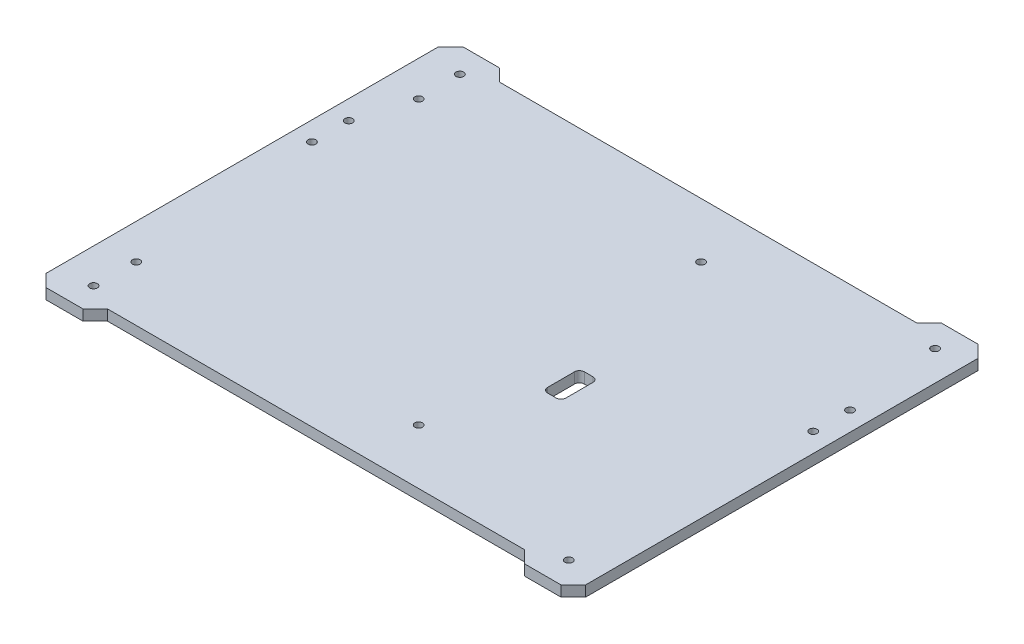
SolidWorks part; units mm, degrees
ref_plane "Front Plane" through (0, 0, 0) normal (0, 0, 1) x (1, 0, 0)
ref_plane "Top Plane" through (0, 0, 0) normal (0, 1, 0) x (1, 0, 0)
ref_plane "Right Plane" through (0, 0, 0) normal (1, 0, 0) x (0, 0, -1)
sketch "Sketch1" plane through (0, 0, 0) normal (0, 1, 0) x (1, 0, 0)
  line L1 (0, 0) -> (279.4, 0)
  line L2 (0, 0) -> (0, 215.9)
  line L3 (0, 215.9) -> (279.4, 215.9)
  line L4 (279.4, 0) -> (279.4, 215.9)
  dimension "D1" = 279.4
  dimension "D2" = 215.9
extrude "Boss-Extrude1" add sketch "Sketch1" along normal blind 5.5118
hole_wizard "5/32 (0.15625) Diameter Hole1" positions "Sketch3" profile "Sketch2" hole size "5/32" standard "ANSI Inch" end condition through all
sketch "Sketch3" plane through (0, 5.5118, 0) normal (0, 1, 0) x (1, 0, 0)
  line L0 (0, 0) -> (279.4, 0) construction
  line L1 (0, 215.9) -> (0, 0) construction
  line L2 (279.4, 215.9) -> (0, 215.9) construction
  line L3 (139.7, 215.9) -> (139.7, 0) construction
  point P0 (17.8594, 13.0969)
  point P7 (17.8594, 202.8031)
  point P9 (9.9219, 153.1938)
  point P11 (9.9219, 134.1438)
  point P27 (263.9219, 13.0969)
  point P28 (269.4781, 134.1438)
  point P29 (269.4781, 153.1938)
  point P30 (263.9219, 202.8031)
  dimension "D1" = 13.0969
  dimension "D2" = 134.1438
  dimension "D3" = 19.05
  dimension "D4" = 9.9219
  dimension "D5" = 13.0969
  dimension "D6" = 17.8594
  dimension "D7" = 246.0625
sketch "Sketch2" plane through (17.8594, 5.5118, -13.0969) normal (1, 0, 0) x (0, 0, 1)
  line L0 (0, 0) -> (0, 5.5118)
  line L1 (0, 5.5118) -> (1.9844, 5.5118)
  line L2 (1.9844, 5.5118) -> (1.9844, 0)
  line L5 (1.9844, 0) -> (0, 0)
  line L11 (0, -6.35) -> (0, 107.95) construction
  dimension "Thru Hole Dia." = 3.9688
  dimension "Thru Hole Depth" = 5.5118
hole_wizard "5/32 (0.15625) Diameter Hole2" positions "Sketch5" profile "Sketch4" hole size "5/32" standard "ANSI Inch" end condition through all
sketch "Sketch5" plane through (0, 5.5118, 0) normal (0, 1, 0) x (1, 0, 0)
  line L0 (0, 215.9) -> (0, 0) construction
  line L2 (0, 107.95) -> (279.4, 107.95) construction
  line L3 (279.4, 0) -> (279.4, 215.9) construction
  point P0 (18.2563, 34.8361)
  point P2 (164.4841, 34.8361)
  point P17 (164.4841, 181.0639)
  point P18 (18.2563, 181.0639)
  dimension "D1" = 18.2562
  dimension "D2" = 146.2278
  dimension "D3" = 73.1139
sketch "Sketch4" plane through (18.2563, 5.5118, -34.8361) normal (1, 0, 0) x (0, 0, 1)
  line L0 (0, 0) -> (0, 5.5118)
  line L1 (0, 5.5118) -> (1.9844, 5.5118)
  line L2 (1.9844, 5.5118) -> (1.9844, 0)
  line L5 (1.9844, 0) -> (0, 0)
  line L11 (0, -6.35) -> (0, 107.95) construction
  dimension "Thru Hole Dia." = 3.9688
  dimension "Thru Hole Depth" = 5.5118
sketch "Sketch6" plane through (0, 5.5118, 0) normal (0, 1, 0) x (1, 0, 0)
  line L0 (279.4, 215.9) -> (0, 215.9) construction
  line L4 (279.4, 215.9) -> (0, 215.9)
  line L5 (0, 107.95) -> (279.4, 107.95) construction
  line L6 (0, 215.9) -> (0, 0) construction
  line L7 (279.4, 0) -> (279.4, 215.9) construction
  line L8 (247.65, 209.55) -> (31.75, 209.55)
  line L9 (254, 0) -> (247.65, 6.35)
  line L10 (25.4, 0) -> (31.75, 6.35)
  line L11 (247.65, 6.35) -> (31.75, 6.35)
  line L12 (25.4, 215.9) -> (31.75, 209.55)
  line L13 (254, 215.9) -> (247.65, 209.55)
  line L14 (273.05, 209.55) -> (6.35, 209.55) construction
  line L15 (279.4, 0) -> (0, 0)
  line L16 (6.35, 209.55) -> (6.35, 6.35) construction
  line L17 (0, 215.9) -> (0, 0) construction
  line L18 (6.35, 6.35) -> (273.05, 6.35) construction
  line L19 (0, 0) -> (279.4, 0) construction
  line L20 (273.05, 6.35) -> (273.05, 209.55) construction
  line L21 (279.4, 0) -> (279.4, 215.9) construction
  line M14 (0, 0) -> (279.4, 0)
  dimension "D2" = 25.4
  dimension "D3" = 45
  dimension "D4" = 25.4
  dimension "D5" = 45
  dimension "D1" = 6.35
extrude "Cut-Extrude2" cut sketch "Sketch6" along direction (0, -1, 0) on the side against the normal through all contours L13 L4 L12 L8 | L9 L11 L10 M14
chamfer "Chamfer1" distance 6.35 angle 45 4 edges at (279.4, 2.7559, -215.9) (279.4, 2.7559, 0) (0, 2.7559, 0) (0, 2.7559, -215.9)
sketch "Sketch7" plane through (0, 5.5118, 0) normal (0, 1, 0) x (1, 0, 0)
  line L0 (247.65, 6.35) -> (31.75, 6.35) construction
  line L1 (183.515, 101.6) -> (187.96, 101.6)
  line L2 (180.975, 99.06) -> (180.975, 85.09)
  line L3 (183.515, 82.55) -> (187.96, 82.55)
  line L4 (190.5, 99.06) -> (190.5, 85.09)
  line L5 (279.4, 6.35) -> (279.4, 209.55) construction
  arc A0 (180.975, 85.09) -> (183.515, 82.55) centre (183.515, 85.09) ccw
  arc A1 (187.96, 82.55) -> (190.5, 85.09) centre (187.96, 85.09) ccw
  arc A2 (187.96, 101.6) -> (190.5, 99.06) centre (187.96, 99.06) cw
  arc A3 (183.515, 101.6) -> (180.975, 99.06) centre (183.515, 99.06) ccw
  point P10 (180.975, 82.55)
  point P15 (190.5, 101.6)
  point P18 (180.975, 101.6)
  dimension "D5" = 2.54
  dimension "D1" = 76.2
  dimension "D2" = 88.9
  dimension "D3" = 19.05
  dimension "D4" = 9.525
extrude "Cut-Extrude3" cut sketch "Sketch7" against normal through all
